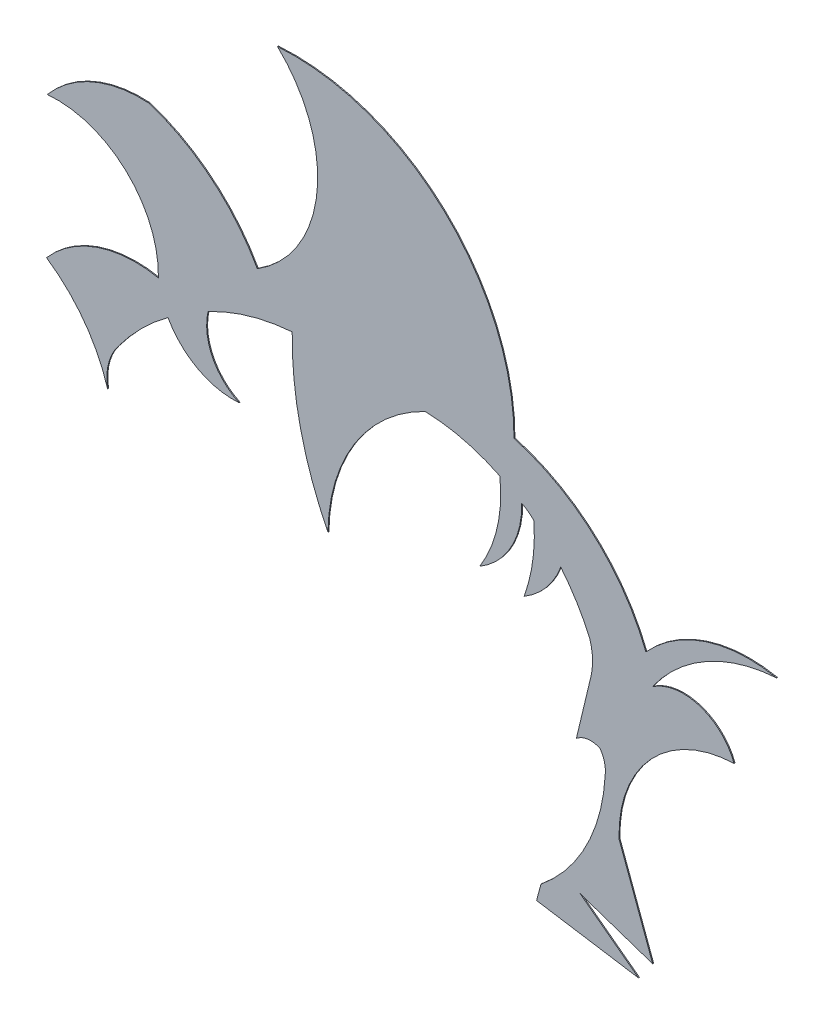
SolidWorks part; units mm, degrees
ref_plane "Alzado" through (0, 0, 0) normal (0, 0, 1) x (1, 0, 0)
ref_plane "Planta" through (0, 0, 0) normal (0, 1, 0) x (1, 0, 0)
ref_plane "Vista lateral" through (0, 0, 0) normal (1, 0, 0) x (0, 0, -1)
sketch "Model" plane through (0, 0, 0) normal (0, 0, 1) x (1, 0, 0)
  line L0 (46.7813, 16.1634) -> (45.2106, 9.5972)
  line L1 (41.4146, -5.822) -> (40.9431, -7.5745)
  line L2 (49.7866, 2.5331) -> (53.3878, -7.2317)
  line L3 (45.6103, -4.6015) -> (53.3878, -7.2317)
  line L4 (45.6103, -4.6015) -> (51.8748, -9.2999)
  line L5 (51.8748, -9.2999) -> (40.9431, -7.5745)
  arc A0 (-3.8625, 21.4535) -> (-5.0133, 16.9152) centre (0.6088, 17.9046) ccw
  arc A1 (1.4531, 26.7697) -> (-3.8625, 21.4535) centre (16.3521, 6.5568) ccw
  arc A2 (1.4531, 26.7697) -> (9.0785, 22.6737) centre (8.4638, 30.6753) ccw
  arc A3 (5.7474, 29.4736) -> (9.0785, 22.6737) centre (11.6186, 28.1339) ccw
  arc A4 (14.7652, 32.0959) -> (5.7474, 29.4736) centre (16.5442, 9.161) ccw
  arc A5 (14.7652, 32.0959) -> (18.5957, 15.421) centre (50.4339, 31.5124) ccw
  arc A6 (29.0123, 31.8344) -> (18.5957, 15.421) centre (37.091, 15.1953) ccw
  arc A7 (37.0108, 29.8435) -> (29.0123, 31.8344) centre (28.4564, 12.5382) ccw
  arc A8 (34.8589, 20.3965) -> (37.0108, 29.8435) centre (22.4456, 28.1927) ccw
  arc A9 (34.8589, 20.3965) -> (39.3566, 28.4811) centre (30.2435, 28.2575) ccw
  arc A10 (40.6571, 27.5258) -> (39.3566, 28.4811) centre (37.5328, 24.6356) ccw
  arc A11 (39.6136, 19.9878) -> (40.6571, 27.5258) centre (22.54, 26.1925) ccw
  arc A12 (39.6136, 19.9878) -> (43.5385, 24.6517) centre (35.0245, 27.8331) ccw
  arc A13 (46.6372, 19.6046) -> (43.5385, 24.6517) centre (26.8035, 10.9022) ccw
  arc A14 (46.7813, 16.1634) -> (46.6372, 19.6046) centre (40.3508, 17.6178) ccw
  arc A15 (47.7456, 9.9358) -> (45.2106, 9.5972) centre (46.7435, 7.7798) ccw
  arc A16 (48.2936, 7.711) -> (47.7456, 9.9358) centre (45.1424, 8.1147) ccw
  arc A17 (41.4146, -5.822) -> (48.2936, 7.711) centre (29.6684, 8.6636) ccw
  arc A18 (-5.0133, 16.9152) -> (-11.5588, 25.8198) centre (-20.7852, 12.1798) ccw
  arc A19 (0.4307, 29.9334) -> (-11.5588, 25.8198) centre (-2.0372, 17.5973) ccw
  arc A20 (0.4307, 29.9334) -> (-11.4741, 41.0018) centre (-10.4607, 30.1553) ccw
  arc A21 (-0.5492, 45.6417) -> (-11.4741, 41.0018) centre (-1.4326, 32.54) ccw
  arc A22 (11.0276, 36.0833) -> (-0.5492, 45.6417) centre (-6.9647, 26.0814) ccw
  arc A23 (11.0276, 36.0833) -> (13.1858, 57.7811) centre (3.7102, 47.7674) ccw
  arc A24 (38.5267, 34.0949) -> (13.1858, 57.7811) centre (14.8667, 34.1808) ccw
  arc A25 (52.6612, 21.3516) -> (38.5267, 34.0949) centre (32.7284, 13.4532) ccw
  arc A26 (66.6565, 25.9328) -> (52.6612, 21.3516) centre (63.6686, 11.3929) ccw
  arc A27 (66.6565, 25.9328) -> (53.3636, 18.4808) centre (67.7871, 8.3343) ccw
  arc A28 (62.1088, 15.7221) -> (53.3636, 18.4808) centre (56.6489, 13.6546) ccw
  arc A29 (62.1088, 15.7221) -> (49.7866, 2.5331) centre (62.5219, 2.9855) ccw
extrude "Saliente-Extruir1" add sketch "Model" along normal blind 0.1
